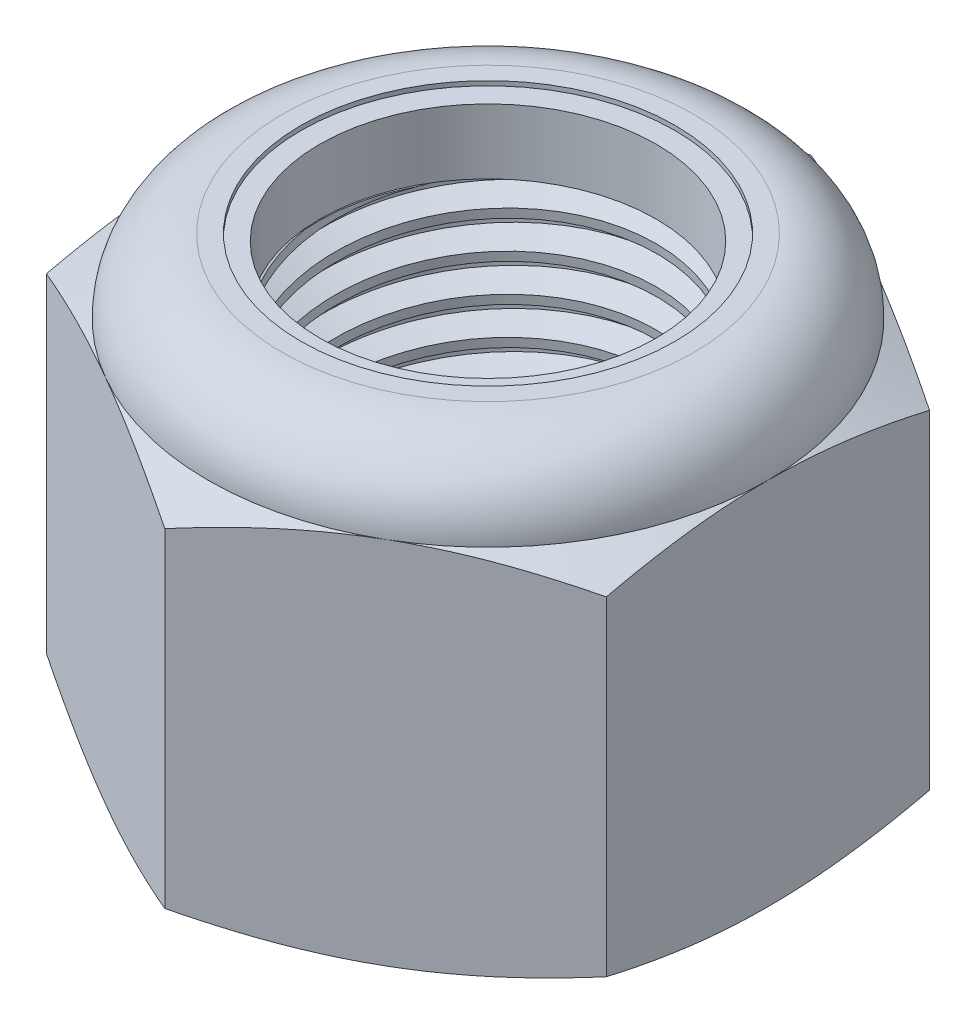
SolidWorks part; units mm, degrees
material "Plain Carbon Steel"
ref_plane "Front" through (0, 0, 0) normal (0, 0, 1) x (1, 0, 0)
ref_plane "Top" through (0, 0, 0) normal (0, 1, 0) x (1, 0, 0)
ref_plane "Right" through (0, 0, 0) normal (1, 0, 0) x (0, 0, -1)
sketch "Sketch1" plane through (0, 0, 0) normal (0, 1, 0) x (1, 0, 0)
  line L1 (0, 10.9985) -> (-9.525, 5.4993)
  line L2 (-9.525, 5.4993) -> (-9.525, -5.4993)
  line L3 (-9.525, -5.4993) -> (0, -10.9985)
  line L4 (0, -10.9985) -> (9.525, -5.4993)
  line L5 (9.525, -5.4993) -> (9.525, 5.4993)
  line L6 (9.525, 5.4993) -> (0, 10.9985)
  circle A0 centre (0, 0) radius 9.525 construction
  dimension "Hex Flats" = 19.05
extrude "Extrude1" add sketch "Sketch1" along normal blind 15.0812
sketch "Sketch2" plane through (0, 0, 0) normal (1, 0, 0) x (0, 0, -1)
  line L0 (-6.35, 0) -> (-6.35, 15.0812) construction
  line L1 (0, 0) -> (6.35, 0)
  line L2 (0, 0) -> (0, 15.0812)
  line L3 (0, 15.0812) -> (6.35, 15.0812)
  line L4 (6.35, 0) -> (6.35, 15.0812)
  line L5 (-5.4993, 15.0812) -> (5.4993, 15.0812) construction
  line L7 (0, -6.35) -> (0, 0) construction
  dimension "Thread Dia" = 12.7
revolve "Revolve1" add sketch "Sketch2" angle 360 about L7
sketch "Sketch3" plane through (0, 0, 0) normal (1, 0, 0) x (0, 0, -1)
  line L0 (6.35, 15.0813) -> (-6.35, 15.0812) construction
  line L1 (-6.35, 15.0812) -> (-6.35, 13.8113) construction
  line L2 (-6.35, 13.8113) -> (6.35, 15.0813) construction
  line L3 (6.35, 15.0813) -> (6.3658, 14.9233) construction
  line L4 (6.3658, 14.9233) -> (6.4764, 13.8176)
  line L5 (6.4764, 13.8176) -> (5.7529, 14.1441)
  line L6 (5.7529, 14.1441) -> (5.7213, 14.46)
  line L7 (5.7213, 14.46) -> (6.3658, 14.9233)
  line L8 (5.7371, 14.302) -> (6.4211, 14.3704) construction
  line L9 (6.35, 15.0813) -> (6.35, 14.3633) construction
  line L10 (6.35, 14.3633) -> (-6.35, 13.0933) construction
  line L11 (-6.35, 13.0933) -> (-6.35, 13.8113) construction
  line L12 (-0.1353, 15.0813) -> (0.1353, 12.3754) construction
  line L13 (-6.35, 0) -> (-6.35, 15.0812) construction
  line L14 (0, 15.0812) -> (6.35, 15.0812) construction
  line L15 (6.35, 0) -> (6.35, 15.0812) construction
  point P13 (0, 13.7283)
  dimension "D1" = 0.1588
  dimension "D2" = 0.3175
  dimension "Thread Pitch" = 1.27
  dimension "D4" = 60
  dimension "D5" = 1.27
revolve "Cut-Revolve1" cut sketch "Sketch3" angle 360 about L12
pattern_linear "LPattern1" count 12 spacing 1.27 along (0, -1, 0) count 2 spacing 1.27 along (0, 1, 0) of "Cut-Revolve1"
sketch "Sketch4" plane through (0, 0, 0) normal (1, 0, 0) x (0, 0, -1)
  line L0 (0, 15.0812) -> (6.35, 15.0812)
  line L1 (6.35, 15.0812) -> (5.7213, 14.7881)
  line L2 (5.7213, 14.7881) -> (5.7213, 0.2932)
  line L3 (5.7213, 0.2932) -> (6.35, 0)
  line L4 (6.35, 0) -> (0, 0)
  line L5 (0, 0) -> (0, 15.0812)
  line L6 (6.35, 0) -> (6.35, 15.0812) construction
  line L7 (0, 15.0812) -> (6.35, 15.0812) construction
  line L8 (0, 0) -> (6.35, 0) construction
  line L9 (0, 0) -> (0, 15.0812) construction
  line L10 (0, 15.0812) -> (0, 15.775) construction
  dimension "D1" = 25
revolve "Cut-Revolve2" cut sketch "Sketch4" angle 360 about L10
combine bodies "Combine1" operation type subtract main body 112 bodies to subtract 111
sketch "Sketch5" plane through (0, 0, 0) normal (1, 0, 0) x (0, 0, -1)
  line L0 (0, 0) -> (9.525, 0)
  line L1 (9.525, 0) -> (10.9985, 0.6871)
  line L2 (10.9985, 0.6871) -> (10.9985, 11.8806)
  line L3 (10.9985, 11.8806) -> (9.525, 12.5677)
  line L4 (7.0115, 15.0813) -> (7.0115, 16.3513)
  line L5 (7.0115, 16.3513) -> (12.2685, 16.3513)
  line L6 (12.2685, 16.3513) -> (12.2685, -1.27)
  line L7 (12.2685, -1.27) -> (0, -1.27)
  line L8 (0, -1.27) -> (0, 0)
  line L9 (9.525, 12.5677) -> (9.525, 0) construction
  line L10 (0, 0) -> (6.35, 0) construction
  line L13 (10.9985, 6.2839) -> (12.2685, 6.2839) construction
  line L14 (10.9985, 15.0812) -> (10.9985, 0) construction
  line L15 (0, 0) -> (0, 16.3513) construction
  line L20 (0, 16.3513) -> (7.0115, 16.3513) construction
  line L22 (0, 15.0812) -> (6.35, 15.0812) construction
  arc A0 (9.525, 12.5677) -> (7.0115, 15.0813) centre (7.0115, 12.5677) ccw
  dimension "D1" = 25
  dimension "D2" = 1.27
  dimension "D3" = 15.0813
  dimension "D4" = 2.5135
revolve "Cut-Revolve3" cut sketch "Sketch5" angle 360 about L15
sketch "Sketch6" plane through (0, 0, 0) normal (1, 0, 0) x (0, 0, -1)
  line L0 (0, 12.5677) -> (9.3726, 12.5677)
  line L1 (7.0115, 14.9289) -> (6.3664, 14.9289)
  line L2 (0, 16.3513) -> (0, 12.5677)
  line L3 (6.3664, 16.3513) -> (0, 16.3513)
  line L4 (0, 16.3513) -> (7.0115, 16.3513) construction
  line L5 (0, 0) -> (0, 16.3513) construction
  line L6 (0, 16.3513) -> (0, 44.323) construction
  line L7 (6.3664, 14.9289) -> (6.3664, 16.3513)
  line L8 (7.0115, 15.0813) -> (7.0115, 14.9289) construction
  line L9 (6.3664, 14.9289) -> (5.7213, 14.9289) construction
  line L10 (5.7213, 14.9289) -> (5.7213, 14.7881) construction
  arc A0 (9.3726, 12.5677) -> (7.0115, 14.9289) centre (7.0115, 12.5677) ccw
  arc A1 (9.525, 12.5677) -> (7.0115, 15.0813) centre (7.0115, 12.5677) ccw construction
  dimension "D1" = 0.1524
revolve "Cut-Revolve4" cut sketch "Sketch6" angle 360 about L6
sketch "Sketch7" plane through (0, 0, 0) normal (1, 0, 0) x (0, 0, -1)
  line L0 (5.7213, 12.6439) -> (9.2951, 12.6439)
  line L1 (7.0115, 14.8527) -> (5.7213, 14.8527)
  line L2 (5.7213, 14.8527) -> (5.7213, 12.6439)
  line L3 (5.7213, 12.6439) -> (0, 12.6439) construction
  line L4 (0, 12.6439) -> (0, 14.8527) construction
  line L5 (0, 14.8527) -> (5.7213, 14.8527) construction
  line L6 (5.7213, 12.6439) -> (5.7213, 12.5677) construction
  line L7 (0, 12.5677) -> (9.3726, 12.5677) construction
  line L8 (7.0115, 14.8527) -> (7.0115, 14.9289) construction
  arc A0 (9.2951, 12.6439) -> (7.0115, 14.8527) centre (7.0115, 12.5677) ccw
  arc A2 (9.3726, 12.5677) -> (7.0115, 14.9289) centre (7.0115, 12.5677) ccw construction
  dimension "D1" = 0.0762
revolve "Revolve2" add sketch "Sketch7" angle 360 about L4
equation "\"D1@Sketch3\"=\"Thread Pitch@Sketch3\"/8"
equation "\"D2@Sketch3\"=\"Thread Pitch@Sketch3\"/4"
equation "\"D5@Sketch3\"=\"Thread Pitch@Sketch3\""
equation "\"D4@LPattern1\"=\"Thread Pitch@Sketch3\""
equation "\"D3@LPattern1\"=\"Thread Pitch@Sketch3\""
equation "\"D1@LPattern1\"=\"Height@Extrude1\"/\"Thread Pitch@Sketch3\""
equation "\"D4@Sketch5\"=\"Height@Extrude1\"/6"
